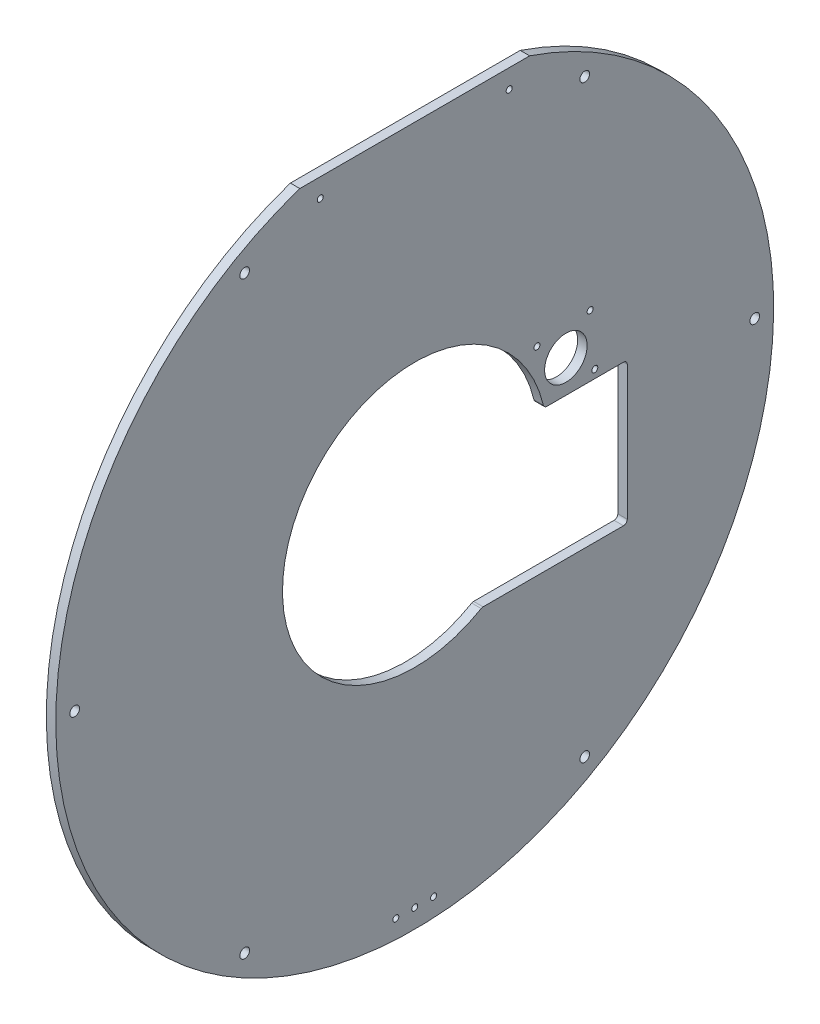
SolidWorks part; units mm, degrees
ref_plane "Front Plane" through (0, 0, 0) normal (0, 0, 1) x (1, 0, 0)
ref_plane "Top Plane" through (0, 0, 0) normal (0, 1, 0) x (1, 0, 0)
ref_plane "Right Plane" through (0, 0, 0) normal (1, 0, 0) x (0, 0, -1)
sketch "Sketch1" plane through (0, 0, 0) normal (1, 0, 0) x (0, 0, -1)
  line L0 (0, 0) -> (-228.6, 0) construction
  line L1 (-77.2511, 228.6) -> (77.2511, 228.6)
  line L2 (-241.3, 0) -> (241.3, 0) construction
  line L3 (0, 241.3) -> (0, -241.3) construction
  line L4 (101.6, 40.64) -> (82.1425, 56.9668) construction
  line L5 (101.6, 40.64) -> (82.1425, 56.9668) construction
  line L6 (0, 0) -> (101.6, 40.64) construction
  line L7 (60.325, -76.5225) -> (45.2496, -76.5225)
  line L8 (60.325, 18.7275) -> (142.875, 18.7275)
  line L9 (60.325, 18.7275) -> (60.325, -76.5225)
  line L10 (60.325, -76.5225) -> (142.875, -76.5225)
  line L11 (142.875, 18.7275) -> (142.875, -76.5225)
  circle A0 centre (0, 0) radius 241.3
  circle A1 centre (0, 0) radius 88.9
  circle A2 centre (-228.6, 0) radius 3.2639
  circle A3 centre (-114.3, 197.9734) radius 3.2639
  circle A4 centre (114.3, 197.9734) radius 3.2639
  circle A5 centre (228.6, 0) radius 3.2639
  circle A6 centre (114.3, -197.9734) radius 3.2639
  circle A7 centre (-114.3, -197.9734) radius 3.2639
  circle A8 centre (0, -228.6) radius 2.0193
  circle A9 centre (-12.7, -228.6) radius 2.0193
  circle A10 centre (-63.5, 215.9) radius 2.0193
  circle A11 centre (63.5, 215.9) radius 2.0193
  circle A12 centre (12.7, -228.6) radius 2.0193
  circle A13 centre (101.6, 40.64) radius 14.2875
  circle A14 centre (82.1425, 56.9668) radius 2.0193
  circle A15 centre (117.9268, 60.0975) radius 2.0193
  circle A16 centre (121.0575, 24.3132) radius 2.0193
  circle A18 centre (85.2732, 21.1825) radius 2.0193 [skipped]
  point P51 (101.6, 18.7275)
  dimension "D1" = 482.6
  dimension "D2" = 177.8
  dimension "D4" = 6.5278
  dimension "D9" = 4.0386
  dimension "D10" = 4.0386
  dimension "D12" = 63.5
  dimension "D14" = 4.0386
  dimension "D17" = 28.575
  dimension "D19" = 4.0386
  dimension "D3" = 228.6
  dimension "D6" = 228.6
  dimension "D7" = 228.6
  dimension "D8" = 228.6
  dimension "D11" = 12.7
  dimension "D13" = 215.9
  dimension "D15" = 40.64
  dimension "D16" = 101.6
  dimension "D18" = 25.4
  dimension "D21" = 25.4
  dimension "D22" = 82.55
  dimension "D23" = 95.25
  dimension "D24" = 101.6
  dimension "D5" = 6
  dimension "D20" = 4
extrude "Boss-Extrude1" add sketch "Sketch1" along normal blind 6.35 contours L1 A0 A16 A15 A14 A13 A11 A10 A9 A8 A7 A6 A5 A4 A3 A2 A1 A12
fillet "Fillet1" radius 2.54 4 edges at (3.175, 18.7275, -86.9051) (3.175, 18.7275, -142.875) (3.175, -76.5225, -142.875) (3.175, -76.5225, -45.2496)
